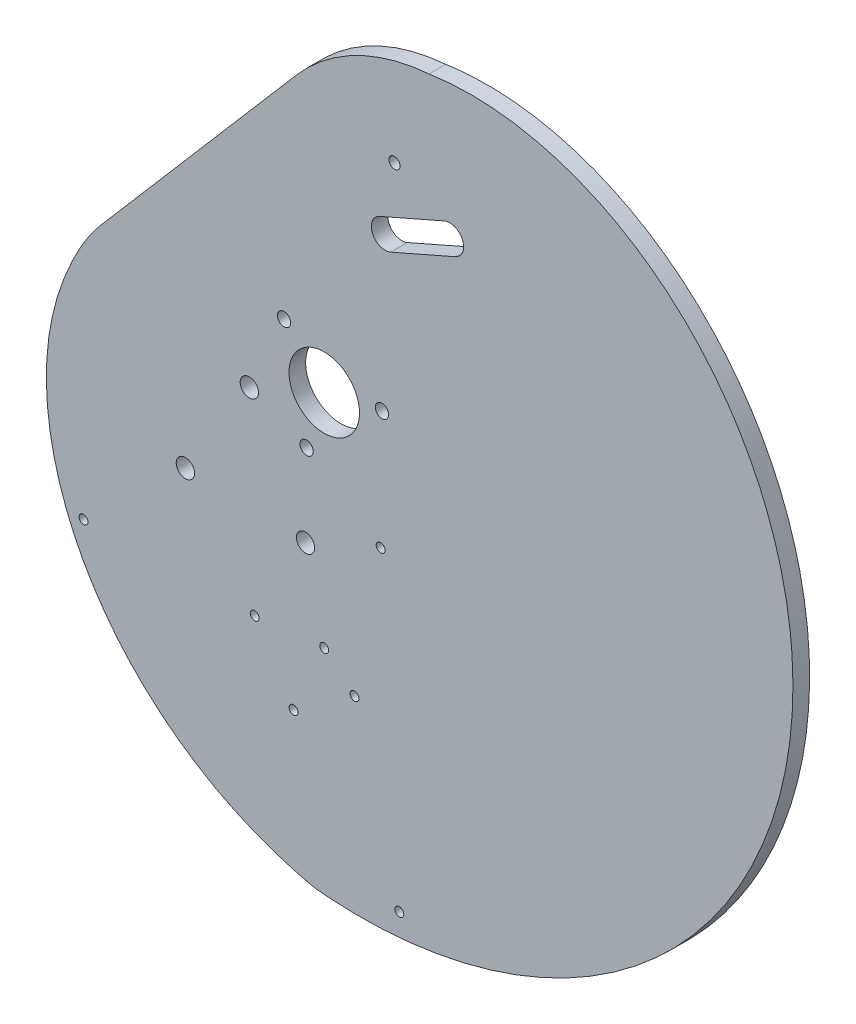
SolidWorks part; units mm, degrees
ref_plane "Front Plane" through (0, 0, 0) normal (0, 0, 1) x (1, 0, 0)
ref_plane "Top Plane" through (0, 0, 0) normal (0, 1, 0) x (1, 0, 0)
ref_plane "Right Plane" through (0, 0, 0) normal (1, 0, 0) x (0, 0, -1)
curve "Curve1"
sketch "Sketch1" plane through (0, 0, 0) normal (0, 0, 1) x (1, 0, 0)
  line L0 (10.9805, 30.1851) -> (22.6104, 35.2876) construction
  line L1 (9.976, 32.4744) -> (21.6059, 37.5769)
  line L2 (11.9849, 27.8957) -> (23.6148, 32.9983)
  line L3 (10.7688, 46.4724) -> (16.7954, 32.7363) construction
  line L4 (-15.5247, -36.542) -> (-17.0714, -47.8252) construction
  line L5 (-12.072, -37.0153) -> (-13.6188, -48.2986) construction
  line L6 (-18.9773, -36.0687) -> (-20.5241, -47.3519) construction
  line L7 (-15.1851, -34.0651) -> (-15.8642, -39.0188) construction
  line L8 (5.6152, 38.2953) -> (3.8561, 42.4197)
  line L9 (20.342, 44.5764) -> (18.4912, 48.9157)
  circle A0 centre (0, 0) radius 6.35
  arc A1 (9.976, 32.4744) -> (11.9849, 27.8957) centre (10.9805, 30.1851) ccw
  arc A2 (23.6148, 32.9983) -> (21.6059, 37.5769) centre (22.6104, 35.2876) ccw
  arc A3 (5.6152, 38.2953) -> (20.342, 44.5764) centre (12.9786, 41.4359) ccw
  arc A4 (-12.072, -37.0153) -> (-18.9773, -36.0687) centre (-15.5247, -36.542) ccw construction
  arc A5 (-20.5241, -47.3519) -> (-13.6188, -48.2986) centre (-17.0714, -47.8252) ccw construction
  spline S0 degree 3 poles (-1.1843, -67.9504) (-0.014, -68.2767) (1.195, -68.3213) (2.3889, -68.4148) (3.5889, -68.4701) (4.791, -68.5105) (5.9959, -68.5295) (7.203, -68.5287) (8.412, -68.5074) (9.6226, -68.4657) (10.8344, -68.4032) (12.047, -68.32) (13.2602, -68.2159) (14.4735, -68.0908) (15.6866, -67.9446) (16.8991, -67.777) (18.1106, -67.5882) (19.3207, -67.3779) (20.529, -67.1461) (21.7351, -66.8927) (22.9386, -66.6176) (24.1392, -66.3208) (25.3362, -66.0022) (26.5295, -65.6619) (27.7184, -65.2996) (28.9026, -64.9155) (30.0816, -64.5096) (31.2551, -64.0817) (32.4225, -63.632) (33.5833, -63.1604) (34.7372, -62.667) (35.8837, -62.1518) (37.0223, -61.6149) (38.1525, -61.0563) (39.2739, -60.4761) (40.3861, -59.8743) (41.4885, -59.2512) (42.5806, -58.6068) (43.6621, -57.9411) (44.7324, -57.2544) (45.791, -56.5468) (46.8375, -55.8184) (47.8714, -55.0695) (48.8923, -54.3001) (49.8996, -53.5105) (50.8929, -52.7009) (51.8717, -51.8715) (52.8356, -51.0225) (53.7841, -50.1542) (54.7166, -49.2668) (55.6329, -48.3607) (56.5323, -47.436) (57.4145, -46.4932) (58.279, -45.5324) (59.1254, -44.554) (59.9531, -43.5583) (60.7619, -42.5458) (61.5512, -41.5167) (62.3207, -40.4714) (63.0698, -39.4103) (63.7983, -38.3338) (64.5057, -37.2423) (65.1916, -36.1362) (65.8556, -35.016) (66.4973, -33.882) (67.1165, -32.7348) (67.7126, -31.5748) (68.2854, -30.4026) (68.8345, -29.2185) (69.3596, -28.023) (69.8603, -26.8168) (70.3364, -25.6003) (70.7876, -24.3741) (71.2134, -23.1386) (71.6138, -21.8945) (71.9884, -20.6423) (72.337, -19.3826) (72.6592, -18.116) (72.955, -16.843) (73.224, -15.5643) (73.4661, -14.2804) (73.6812, -12.992) (73.8689, -11.6997) (74.0292, -10.4042) (74.1619, -9.106) (74.2669, -7.8058) (74.3441, -6.5043) (74.3933, -5.2021) (74.4146, -3.9) (74.4078, -2.5984) (74.3729, -1.2982) (74.3098, -0.0001) (74.2186, 1.2954) (74.0993, 2.5875) (73.9518, 3.8756) (73.7762, 5.1589) (73.5725, 6.4367) (73.3409, 7.7084) (73.0814, 8.9732) (72.7942, 10.2305) (72.4792, 11.4795) (72.1368, 12.7196) (71.767, 13.95) (71.3701, 15.1701) (70.9462, 16.3792) (70.4955, 17.5765) (70.0184, 18.7613) (69.515, 19.9331) (68.9856, 21.091) (68.4305, 22.2344) (67.85, 23.3626) (67.2445, 24.475) (66.6143, 25.5709) (65.9598, 26.6495) (65.2813, 27.7103) (64.5793, 28.7526) (63.8542, 29.7758) (63.1064, 30.7792) (62.3364, 31.7621) (61.5447, 32.7241) (60.7318, 33.6643) (59.8981, 34.5824) (59.0442, 35.4776) (58.1707, 36.3494) (57.2782, 37.1972) (56.3671, 38.0204) (55.4383, 38.8186) (54.4923, 39.5913) (53.53, 40.3381) (52.552, 41.0585) (51.5591, 41.7521) (50.552, 42.4186) (49.5315, 43.0576) (48.4984, 43.6687) (47.4535, 44.2516) (46.3974, 44.8061) (45.3311, 45.3318) (44.2553, 45.8284) (43.1709, 46.2958) (42.0786, 46.7338) (40.9793, 47.1421) (39.8737, 47.5205) (38.7628, 47.869) (37.6473, 48.1874) (36.5281, 48.4755) (35.4061, 48.7334) (34.282, 48.961) (33.1567, 49.1581) (32.031, 49.3249) (30.9059, 49.4613) (29.7821, 49.5673) (28.6604, 49.6431) (27.5418, 49.6886) (26.427, 49.7041) (25.3169, 49.6895) (24.2124, 49.6451) (23.1141, 49.571) (22.0231, 49.4674) (20.94, 49.3346) (19.8657, 49.1727) (18.801, 48.982) (17.7468, 48.7628) (16.7037, 48.5154) (15.6726, 48.2401) (14.6543, 47.9373) (13.6495, 47.6073) (12.659, 47.2504) (11.6836, 46.8672) (10.7239, 46.458) (9.7807, 46.0233) (8.8547, 45.5635) (7.9467, 45.0791) (7.0573, 44.5706) (6.1871, 44.0386) (5.3369, 43.4835) (4.5074, 42.906) (3.699, 42.3065) (2.9126, 41.6858) (2.1491, 41.0448) (1.4087, 40.3857) (0.692, 39.711) (-0.0007, 39.0233) (-0.6692, 38.3252) (-1.3135, 37.6192) (-1.9336, 36.908) (-2.5298, 36.194) (-3.1024, 35.4799) (-3.6521, 34.7682) (-4.1795, 34.0612) (-4.6854, 33.3616) (-5.1709, 32.6716) (-5.637, 31.9937) (-6.085, 31.3301) (-6.5163, 30.6831) (-6.9325, 30.0548) (-7.3352, 29.4474) (-7.7263, 28.8629) (-8.1078, 28.3032) (-8.4816, 27.77) (-8.8501, 27.2652) (-9.216, 26.7897) (-9.5801, 26.3424) (-9.9432, 25.9213) (-10.3062, 25.5243) (-10.6698, 25.1494) (-11.0346, 24.7946) (-11.4009, 24.4578) (-11.7691, 24.1369) (-12.1394, 23.8299) (-12.5117, 23.5348) (-12.8861, 23.2497) (-13.2622, 22.9725) (-13.6397, 22.7014) (-14.0182, 22.4345) (-14.3971, 22.1699) (-14.7757, 21.906) (-15.1531, 21.6409) (-15.5285, 21.3732) (-15.9009, 21.1012) (-16.269, 20.8234) (-16.6317, 20.5384) (-16.9875, 20.2449) (-17.3351, 19.9417) (-17.6745, 19.6295) (-18.0059, 19.3089) (-18.3295, 18.9807) (-18.6455, 18.6455) (-18.9542, 18.3039) (-19.2559, 17.9565) (-19.5509, 17.6038) (-19.8396, 17.2464) (-20.1224, 16.8848) (-20.3997, 16.5195) (-20.672, 16.1508) (-20.9397, 15.7793) (-21.2033, 15.4052) (-21.4634, 15.0289) (-21.7205, 14.6507) (-21.9753, 14.2708) (-22.2281, 13.8895) (-22.4798, 13.507) (-22.7308, 13.1233) (-22.9819, 12.7386) (-23.2336, 12.3529) (-23.4866, 11.9663) (-23.7416, 11.5787) (-23.9993, 11.19) (-24.2602, 10.8001) (-24.5251, 10.4088) (-24.7947, 10.016) (-25.0696, 9.6214) (-25.3504, 9.2246) (-25.6379, 8.8254) (-25.9327, 8.4234) (-26.2354, 8.018) (-26.5467, 7.609) (-26.8672, 7.1956) (-27.1974, 6.7776) (-27.537, 6.3539) (-27.8856, 5.9238) (-28.2424, 5.4864) (-28.6069, 5.0408) (-28.9783, 4.5865) (-29.3562, 4.1226) (-29.7396, 3.6485) (-30.1278, 3.1637) (-30.5202, 2.6674) (-30.9158, 2.1592) (-31.314, 1.6386) (-31.7137, 1.1051) (-32.1143, 0.5583) (-32.5148, -0.0021) (-32.9143, -0.5765) (-33.3119, -1.1651) (-33.7067, -1.7682) (-34.0978, -2.3859) (-34.4843, -3.0184) (-34.8652, -3.6658) (-35.2396, -4.3281) (-35.6066, -5.0053) (-35.9651, -5.6973) (-36.3143, -6.404) (-36.6531, -7.1254) (-36.9808, -7.8611) (-37.2963, -8.611) (-37.5988, -9.3748) (-37.8873, -10.1521) (-38.1609, -10.9426) (-38.4187, -11.7459) (-38.66, -12.5613) (-38.8837, -13.3886) (-39.0892, -14.2271) (-39.2755, -15.0762) (-39.4422, -15.9354) (-39.589, -16.8043) (-39.7155, -17.6823) (-39.8215, -18.5689) (-39.9067, -19.4636) (-39.9709, -20.366) (-40.0137, -21.2755) (-40.035, -22.1916) (-40.0345, -23.1138) (-40.0119, -24.0415) (-39.9672, -24.9742) (-39.9002, -25.9114) (-39.8105, -26.8525) (-39.6982, -27.7969) (-39.563, -28.7442) (-39.4048, -29.6936) (-39.2235, -30.6448) (-39.019, -31.597) (-38.7911, -32.5497) (-38.5399, -33.5023) (-38.2653, -34.4543) (-37.9672, -35.4051) (-37.6456, -36.354) (-37.3004, -37.3005) (-36.9317, -38.2441) (-36.5395, -39.184) (-36.1238, -40.1197) (-35.6847, -41.0507) (-35.2221, -41.9763) (-34.7363, -42.896) (-34.2272, -43.8091) (-33.695, -44.715) (-33.1398, -45.6133) (-32.5617, -46.5032) (-31.9609, -47.3843) (-31.3375, -48.2559) (-30.6917, -49.1174) (-30.0238, -49.9683) (-29.3338, -50.808) (-28.6221, -51.636) (-27.8888, -52.4517) (-27.1343, -53.2545) (-26.3587, -54.0439) (-25.5624, -54.8193) (-24.7457, -55.5802) (-23.9088, -56.3261) (-23.0521, -57.0564) (-22.1759, -57.7707) (-21.2805, -58.4684) (-20.3664, -59.149) (-19.4339, -59.812) (-18.4833, -60.4569) (-17.5151, -61.0833) (-16.5298, -61.6908) (-15.5276, -62.2787) (-14.5091, -62.8467) (-13.4747, -63.3944) (-12.4248, -63.9213) (-11.36, -64.4271) (-10.2807, -64.9112) (-9.1874, -65.3733) (-8.0806, -65.8131) (-6.9608, -66.2301) (-5.8286, -66.6239) (-4.6845, -66.9947) (-3.5289, -67.3403) (-2.3631, -67.6669) (-1.1843, -67.9504) (-0.014, -68.2767) (1.195, -68.3213) knots -0.0101 -0.006743 -0.003377 0 0.00332 0.006645 0.009976 0.013312 0.016655 0.020003 0.023357 0.026716 0.030082 0.033453 0.036831 0.040214 0.043603 0.046998 0.050399 0.053806 0.057218 0.060637 0.064061 0.067491 0.070927 0.074369 0.077816 0.081269 0.084728 0.088192 0.091662 0.095138 0.098619 0.102105 0.105597 0.109094 0.112596 0.116103 0.119615 0.123133 0.126655 0.130182 0.133714 0.137251 0.140792 0.144337 0.147888 0.151442 0.155 0.158563 0.16213 0.1657 0.169275 0.172853 0.176434 0.180019 0.183607 0.187199 0.190793 0.19439 0.19799 0.201593 0.205199 0.208806 0.212416 0.216028 0.219642 0.223258 0.226875 0.230494 0.234115 0.237736 0.241359 0.244982 0.248606 0.252231 0.255856 0.259481 0.263106 0.266731 0.270356 0.273981 0.277605 0.281228 0.28485 0.28847 0.29209 0.295708 0.299324 0.302939 0.306551 0.310161 0.313769 0.317374 0.320976 0.324575 0.328171 0.331763 0.335352 0.338938 0.342519 0.346096 0.349669 0.353237 0.356801 0.360359 0.363913 0.367461 0.371004 0.374541 0.378073 0.381598 0.385117 0.38863 0.392136 0.395636 0.399128 0.402614 0.406092 0.409563 0.413026 0.416482 0.419929 0.423369 0.4268 0.430223 0.433637 0.437043 0.44044 0.443828 0.447206 0.450575 0.453935 0.457284 0.460624 0.463953 0.467272 0.47058 0.473877 0.477164 0.480439 0.483703 0.486955 0.490196 0.493426 0.496643 0.499848 0.503042 0.506223 0.509391 0.512547 0.515691 0.518822 0.52194 0.525045 0.528137 0.531216 0.534282 0.537335 0.540375 0.543401 0.546414 0.549414 0.5524 0.555374 0.558333 0.56128 0.564213 0.567133 0.57004 0.572933 0.575814 0.578681 0.581535 0.584377 0.587205 0.590021 0.592825 0.595616 0.598394 0.60116 0.603911 0.606642 0.60935 0.612032 0.614684 0.617303 0.619884 0.622424 0.62492 0.627367 0.629763 0.632104 0.634387 0.636609 0.638767 0.640858 0.64288 0.644831 0.64671 0.648517 0.65025 0.651911 0.653509 0.655048 0.656538 0.657984 0.659394 0.660772 0.662125 0.663458 0.664774 0.666078 0.667373 0.668662 0.669946 0.671227 0.672507 0.673786 0.675065 0.676344 0.677623 0.678903 0.680182 0.681461 0.68274 0.684019 0.685298 0.686575 0.687853 0.689129 0.690404 0.691679 0.692952 0.694224 0.695495 0.696765 0.698035 0.699304 0.700572 0.70184 0.703109 0.704379 0.705651 0.706925 0.708202 0.709483 0.71077 0.712063 0.713364 0.714674 0.715995 0.717328 0.718676 0.72004 0.721422 0.722825 0.72425 0.7257 0.727177 0.728683 0.730218 0.731784 0.73338 0.735008 0.736668 0.738359 0.740082 0.741837 0.743623 0.745441 0.747291 0.749171 0.751082 0.753022 0.754993 0.756992 0.759021 0.761077 0.76316 0.765271 0.767407 0.769569 0.771756 0.773967 0.776201 0.778458 0.780736 0.783036 0.785357 0.787697 0.790056 0.792433 0.794828 0.797239 0.799666 0.80211 0.804571 0.807047 0.80954 0.812049 0.814575 0.817116 0.819674 0.822248 0.824838 0.827444 0.830066 0.832704 0.835358 0.838027 0.840713 0.843414 0.846131 0.848864 0.851612 0.854376 0.857155 0.859949 0.862759 0.865584 0.868424 0.871279 0.874149 0.877033 0.879933 0.882847 0.885776 0.88872 0.891678 0.89465 0.897636 0.900637 0.903651 0.906679 0.909721 0.912777 0.915847 0.91893 0.922026 0.925135 0.928258 0.931393 0.934541 0.937702 0.940876 0.944062 0.947261 0.950471 0.953694 0.956929 0.960175 0.963433 0.966703 0.969984 0.973276 0.976579 0.979893 0.983218 0.986554 0.9899 0.993257 0.996623 1 1.00332 1.006645 1.009976 only from (0, -68.2309) to (0, -68.2309) construction
  spline S1 degree 3 poles (-1.1843, -67.9504) (-0.014, -68.2767) (1.195, -68.3213) (2.3889, -68.4148) (3.5889, -68.4701) (4.791, -68.5105) (5.9959, -68.5295) (7.203, -68.5287) (8.412, -68.5074) (9.6226, -68.4657) (10.8344, -68.4032) (12.047, -68.32) (13.2602, -68.2159) (14.4735, -68.0908) (15.6866, -67.9446) (16.8991, -67.777) (18.1106, -67.5882) (19.3207, -67.3779) (20.529, -67.1461) (21.7351, -66.8927) (22.9386, -66.6176) (24.1392, -66.3208) (25.3362, -66.0022) (26.5295, -65.6619) (27.7184, -65.2996) (28.9026, -64.9155) (30.0816, -64.5096) (31.2551, -64.0817) (32.4225, -63.632) (33.5833, -63.1604) (34.7372, -62.667) (35.8837, -62.1518) (37.0223, -61.6149) (38.1525, -61.0563) (39.2739, -60.4761) (40.3861, -59.8743) (41.4885, -59.2512) (42.5806, -58.6068) (43.6621, -57.9411) (44.7324, -57.2544) (45.791, -56.5468) (46.8375, -55.8184) (47.8714, -55.0695) (48.8923, -54.3001) (49.8996, -53.5105) (50.8929, -52.7009) (51.8717, -51.8715) (52.8356, -51.0225) (53.7841, -50.1542) (54.7166, -49.2668) (55.6329, -48.3607) (56.5323, -47.436) (57.4145, -46.4932) (58.279, -45.5324) (59.1254, -44.554) (59.9531, -43.5583) (60.7619, -42.5458) (61.5512, -41.5167) (62.3207, -40.4714) (63.0698, -39.4103) (63.7983, -38.3338) (64.5057, -37.2423) (65.1916, -36.1362) (65.8556, -35.016) (66.4973, -33.882) (67.1165, -32.7348) (67.7126, -31.5748) (68.2854, -30.4026) (68.8345, -29.2185) (69.3596, -28.023) (69.8603, -26.8168) (70.3364, -25.6003) (70.7876, -24.3741) (71.2134, -23.1386) (71.6138, -21.8945) (71.9884, -20.6423) (72.337, -19.3826) (72.6592, -18.116) (72.955, -16.843) (73.224, -15.5643) (73.4661, -14.2804) (73.6812, -12.992) (73.8689, -11.6997) (74.0292, -10.4042) (74.1619, -9.106) (74.2669, -7.8058) (74.3441, -6.5043) (74.3933, -5.2021) (74.4146, -3.9) (74.4078, -2.5984) (74.3729, -1.2982) (74.3098, -0.0001) (74.2186, 1.2954) (74.0993, 2.5875) (73.9518, 3.8756) (73.7762, 5.1589) (73.5725, 6.4367) (73.3409, 7.7084) (73.0814, 8.9732) (72.7942, 10.2305) (72.4792, 11.4795) (72.1368, 12.7196) (71.767, 13.95) (71.3701, 15.1701) (70.9462, 16.3792) (70.4955, 17.5765) (70.0184, 18.7613) (69.515, 19.9331) (68.9856, 21.091) (68.4305, 22.2344) (67.85, 23.3626) (67.2445, 24.475) (66.6143, 25.5709) (65.9598, 26.6495) (65.2813, 27.7103) (64.5793, 28.7526) (63.8542, 29.7758) (63.1064, 30.7792) (62.3364, 31.7621) (61.5447, 32.7241) (60.7318, 33.6643) (59.8981, 34.5824) (59.0442, 35.4776) (58.1707, 36.3494) (57.2782, 37.1972) (56.3671, 38.0204) (55.4383, 38.8186) (54.4923, 39.5913) (53.53, 40.3381) (52.552, 41.0585) (51.5591, 41.7521) (50.552, 42.4186) (49.5315, 43.0576) (48.4984, 43.6687) (47.4535, 44.2516) (46.3974, 44.8061) (45.3311, 45.3318) (44.2553, 45.8284) (43.1709, 46.2958) (42.0786, 46.7338) (40.9793, 47.1421) (39.8737, 47.5205) (38.7628, 47.869) (37.6473, 48.1874) (36.5281, 48.4755) (35.4061, 48.7334) (34.282, 48.961) (33.1567, 49.1581) (32.031, 49.3249) (30.9059, 49.4613) (29.7821, 49.5673) (28.6604, 49.6431) (27.5418, 49.6886) (26.427, 49.7041) (25.3169, 49.6895) (24.2124, 49.6451) (23.1141, 49.571) (22.0231, 49.4674) (20.94, 49.3346) (19.8657, 49.1727) (18.801, 48.982) (17.7468, 48.7628) (16.7037, 48.5154) (15.6726, 48.2401) (14.6543, 47.9373) (13.6495, 47.6073) (12.659, 47.2504) (11.6836, 46.8672) (10.7239, 46.458) (9.7807, 46.0233) (8.8547, 45.5635) (7.9467, 45.0791) (7.0573, 44.5706) (6.1871, 44.0386) (5.3369, 43.4835) (4.5074, 42.906) (3.699, 42.3065) (2.9126, 41.6858) (2.1491, 41.0448) (1.4087, 40.3857) (0.692, 39.711) (-0.0007, 39.0233) (-0.6692, 38.3252) (-1.3135, 37.6192) (-1.9336, 36.908) (-2.5298, 36.194) (-3.1024, 35.4799) (-3.6521, 34.7682) (-4.1795, 34.0612) (-4.6854, 33.3616) (-5.1709, 32.6716) (-5.637, 31.9937) (-6.085, 31.3301) (-6.5163, 30.6831) (-6.9325, 30.0548) (-7.3352, 29.4474) (-7.7263, 28.8629) (-8.1078, 28.3032) (-8.4816, 27.77) (-8.8501, 27.2652) (-9.216, 26.7897) (-9.5801, 26.3424) (-9.9432, 25.9213) (-10.3062, 25.5243) (-10.6698, 25.1494) (-11.0346, 24.7946) (-11.4009, 24.4578) (-11.7691, 24.1369) (-12.1394, 23.8299) (-12.5117, 23.5348) (-12.8861, 23.2497) (-13.2622, 22.9725) (-13.6397, 22.7014) (-14.0182, 22.4345) (-14.3971, 22.1699) (-14.7757, 21.906) (-15.1531, 21.6409) (-15.5285, 21.3732) (-15.9009, 21.1012) (-16.269, 20.8234) (-16.6317, 20.5384) (-16.9875, 20.2449) (-17.3351, 19.9417) (-17.6745, 19.6295) (-18.0059, 19.3089) (-18.3295, 18.9807) (-18.6455, 18.6455) (-18.9542, 18.3039) (-19.2559, 17.9565) (-19.5509, 17.6038) (-19.8396, 17.2464) (-20.1224, 16.8848) (-20.3997, 16.5195) (-20.672, 16.1508) (-20.9397, 15.7793) (-21.2033, 15.4052) (-21.4634, 15.0289) (-21.7205, 14.6507) (-21.9753, 14.2708) (-22.2281, 13.8895) (-22.4798, 13.507) (-22.7308, 13.1233) (-22.9819, 12.7386) (-23.2336, 12.3529) (-23.4866, 11.9663) (-23.7416, 11.5787) (-23.9993, 11.19) (-24.2602, 10.8001) (-24.5251, 10.4088) (-24.7947, 10.016) (-25.0696, 9.6214) (-25.3504, 9.2246) (-25.6379, 8.8254) (-25.9327, 8.4234) (-26.2354, 8.018) (-26.5467, 7.609) (-26.8672, 7.1956) (-27.1974, 6.7776) (-27.537, 6.3539) (-27.8856, 5.9238) (-28.2424, 5.4864) (-28.6069, 5.0408) (-28.9783, 4.5865) (-29.3562, 4.1226) (-29.7396, 3.6485) (-30.1278, 3.1637) (-30.5202, 2.6674) (-30.9158, 2.1592) (-31.314, 1.6386) (-31.7137, 1.1051) (-32.1143, 0.5583) (-32.5148, -0.0021) (-32.9143, -0.5765) (-33.3119, -1.1651) (-33.7067, -1.7682) (-34.0978, -2.3859) (-34.4843, -3.0184) (-34.8652, -3.6658) (-35.2396, -4.3281) (-35.6066, -5.0053) (-35.9651, -5.6973) (-36.3143, -6.404) (-36.6531, -7.1254) (-36.9808, -7.8611) (-37.2963, -8.611) (-37.5988, -9.3748) (-37.8873, -10.1521) (-38.1609, -10.9426) (-38.4187, -11.7459) (-38.66, -12.5613) (-38.8837, -13.3886) (-39.0892, -14.2271) (-39.2755, -15.0762) (-39.4422, -15.9354) (-39.589, -16.8043) (-39.7155, -17.6823) (-39.8215, -18.5689) (-39.9067, -19.4636) (-39.9709, -20.366) (-40.0137, -21.2755) (-40.035, -22.1916) (-40.0345, -23.1138) (-40.0119, -24.0415) (-39.9672, -24.9742) (-39.9002, -25.9114) (-39.8105, -26.8525) (-39.6982, -27.7969) (-39.563, -28.7442) (-39.4048, -29.6936) (-39.2235, -30.6448) (-39.019, -31.597) (-38.7911, -32.5497) (-38.5399, -33.5023) (-38.2653, -34.4543) (-37.9672, -35.4051) (-37.6456, -36.354) (-37.3004, -37.3005) (-36.9317, -38.2441) (-36.5395, -39.184) (-36.1238, -40.1197) (-35.6847, -41.0507) (-35.2221, -41.9763) (-34.7363, -42.896) (-34.2272, -43.8091) (-33.695, -44.715) (-33.1398, -45.6133) (-32.5617, -46.5032) (-31.9609, -47.3843) (-31.3375, -48.2559) (-30.6917, -49.1174) (-30.0238, -49.9683) (-29.3338, -50.808) (-28.6221, -51.636) (-27.8888, -52.4517) (-27.1343, -53.2545) (-26.3587, -54.0439) (-25.5624, -54.8193) (-24.7457, -55.5802) (-23.9088, -56.3261) (-23.0521, -57.0564) (-22.1759, -57.7707) (-21.2805, -58.4684) (-20.3664, -59.149) (-19.4339, -59.812) (-18.4833, -60.4569) (-17.5151, -61.0833) (-16.5298, -61.6908) (-15.5276, -62.2787) (-14.5091, -62.8467) (-13.4747, -63.3944) (-12.4248, -63.9213) (-11.36, -64.4271) (-10.2807, -64.9112) (-9.1874, -65.3733) (-8.0806, -65.8131) (-6.9608, -66.2301) (-5.8286, -66.6239) (-4.6845, -66.9947) (-3.5289, -67.3403) (-2.3631, -67.6669) (-1.1843, -67.9504) (-0.014, -68.2767) (1.195, -68.3213) knots -0.0101 -0.006743 -0.003377 0 0.00332 0.006645 0.009976 0.013312 0.016655 0.020003 0.023357 0.026716 0.030082 0.033453 0.036831 0.040214 0.043603 0.046998 0.050399 0.053806 0.057218 0.060637 0.064061 0.067491 0.070927 0.074369 0.077816 0.081269 0.084728 0.088192 0.091662 0.095138 0.098619 0.102105 0.105597 0.109094 0.112596 0.116103 0.119615 0.123133 0.126655 0.130182 0.133714 0.137251 0.140792 0.144337 0.147888 0.151442 0.155 0.158563 0.16213 0.1657 0.169275 0.172853 0.176434 0.180019 0.183607 0.187199 0.190793 0.19439 0.19799 0.201593 0.205199 0.208806 0.212416 0.216028 0.219642 0.223258 0.226875 0.230494 0.234115 0.237736 0.241359 0.244982 0.248606 0.252231 0.255856 0.259481 0.263106 0.266731 0.270356 0.273981 0.277605 0.281228 0.28485 0.28847 0.29209 0.295708 0.299324 0.302939 0.306551 0.310161 0.313769 0.317374 0.320976 0.324575 0.328171 0.331763 0.335352 0.338938 0.342519 0.346096 0.349669 0.353237 0.356801 0.360359 0.363913 0.367461 0.371004 0.374541 0.378073 0.381598 0.385117 0.38863 0.392136 0.395636 0.399128 0.402614 0.406092 0.409563 0.413026 0.416482 0.419929 0.423369 0.4268 0.430223 0.433637 0.437043 0.44044 0.443828 0.447206 0.450575 0.453935 0.457284 0.460624 0.463953 0.467272 0.47058 0.473877 0.477164 0.480439 0.483703 0.486955 0.490196 0.493426 0.496643 0.499848 0.503042 0.506223 0.509391 0.512547 0.515691 0.518822 0.52194 0.525045 0.528137 0.531216 0.534282 0.537335 0.540375 0.543401 0.546414 0.549414 0.5524 0.555374 0.558333 0.56128 0.564213 0.567133 0.57004 0.572933 0.575814 0.578681 0.581535 0.584377 0.587205 0.590021 0.592825 0.595616 0.598394 0.60116 0.603911 0.606642 0.60935 0.612032 0.614684 0.617303 0.619884 0.622424 0.62492 0.627367 0.629763 0.632104 0.634387 0.636609 0.638767 0.640858 0.64288 0.644831 0.64671 0.648517 0.65025 0.651911 0.653509 0.655048 0.656538 0.657984 0.659394 0.660772 0.662125 0.663458 0.664774 0.666078 0.667373 0.668662 0.669946 0.671227 0.672507 0.673786 0.675065 0.676344 0.677623 0.678903 0.680182 0.681461 0.68274 0.684019 0.685298 0.686575 0.687853 0.689129 0.690404 0.691679 0.692952 0.694224 0.695495 0.696765 0.698035 0.699304 0.700572 0.70184 0.703109 0.704379 0.705651 0.706925 0.708202 0.709483 0.71077 0.712063 0.713364 0.714674 0.715995 0.717328 0.718676 0.72004 0.721422 0.722825 0.72425 0.7257 0.727177 0.728683 0.730218 0.731784 0.73338 0.735008 0.736668 0.738359 0.740082 0.741837 0.743623 0.745441 0.747291 0.749171 0.751082 0.753022 0.754993 0.756992 0.759021 0.761077 0.76316 0.765271 0.767407 0.769569 0.771756 0.773967 0.776201 0.778458 0.780736 0.783036 0.785357 0.787697 0.790056 0.792433 0.794828 0.797239 0.799666 0.80211 0.804571 0.807047 0.80954 0.812049 0.814575 0.817116 0.819674 0.822248 0.824838 0.827444 0.830066 0.832704 0.835358 0.838027 0.840713 0.843414 0.846131 0.848864 0.851612 0.854376 0.857155 0.859949 0.862759 0.865584 0.868424 0.871279 0.874149 0.877033 0.879933 0.882847 0.885776 0.88872 0.891678 0.89465 0.897636 0.900637 0.903651 0.906679 0.909721 0.912777 0.915847 0.91893 0.922026 0.925135 0.928258 0.931393 0.934541 0.937702 0.940876 0.944062 0.947261 0.950471 0.953694 0.956929 0.960175 0.963433 0.966703 0.969984 0.973276 0.976579 0.979893 0.983218 0.986554 0.9899 0.993257 0.996623 1 1.00332 1.006645 1.009976 only from (0, -68.2309) to (0, -68.2309)
  point P6 (16.7954, 32.7363)
  point P18 (-16.298, -42.1836)
  dimension "D1" = 12.7
  dimension "D5" = 5.5
  dimension "D2" = 12.7
  dimension "D3" = 5
  dimension "D4" = 15
extrude "Boss-Extrude1" add sketch "Sketch1" along normal mid plane 3 contours A3 S1 A0 A2 L2 A1 L1
sketch "Sketch2" plane through (0, 0, 0) normal (0, 0, 1) x (1, 0, 0)
  line L0 (4.6222, 43.3119) -> (-35.7001, -3.6508) construction
  line L1 (-35.7001, -3.6508) -> (-7.0727, 43.3119)
  line L2 (-7.0727, 43.3119) -> (4.6222, 43.3119)
  line L3 (7.6571, 40.7062) -> (-41.2002, -16.1969)
  line L4 (4.6222, 43.3119) -> (7.6571, 40.7062)
  line L5 (-35.7001, -3.6508) -> (-41.2002, -16.1969)
extrude "Cut-Extrude1" cut sketch "Sketch2" against normal through all both and the other way through all
fillet "Fillet1" radius 20 1 edges at (-38.9189, -13.5399, 0)
sketch "Sketch3" plane through (0, 0, 1.5) normal (0, 0, 1) x (1, 0, 0)
  point P0 (-13.488, -5.936)
  point P1 (-3.3675, -25.0764)
  point P3 (-25.0038, -24.2708)
fillet "Fillet2" [suppressed] radius 2.5
fillet "Fillet3" [suppressed] radius 1
sketch "Sketch6" plane through (0, 0, 0) normal (0, 0, 1) x (1, 0, 0)
  line L2 (-40.2409, 5.985) -> (-5.0109, 47.0167)
  line L3 (-40.2409, 5.985) -> (-5.0109, 47.0167)
  arc A1 (-5.0109, 47.0167) -> (18.8738, 59.1348) centre (21.5961, 24.1717) cw
  arc A2 (-40.2409, 5.985) -> (-43.3928, 1.5586) centre (-17.4796, -13.5579) ccw
  arc A3 (-40.2409, 5.985) -> (-43.3928, 1.5586) centre (-17.4796, -13.5579) ccw
  spline S2 degree 3 poles (30414.9948, -18924.8779) (-757.4347, -1926.1501) (-235.029, 77.1027) (33.4507, 59.3461) (37.0313, 58.7272) (43.9674, 56.8115) (47.3229, 55.515) (53.7078, 52.3312) (56.7371, 50.4441) (62.3895, 46.1692) (65.0134, 43.7791) (69.7846, 38.6064) (71.9342, 35.8236) (75.7327, 29.9643) (77.3816, 26.8878) (80.1644, 20.5326) (81.2983, 17.2539) (83.0485, 10.579) (83.6648, 7.183) (84.3866, 0.3517) (84.4921, -3.0835) (84.2072, -9.921) (83.8168, -13.3233) (82.562, -20.0286) (81.6977, -23.3317) (78.4358, -33.0013) (75.367, -39.1258) (67.7295, -50.3171) (63.1613, -55.384) (52.8841, -64.1458) (47.1758, -67.8403) (35.0265, -73.6501) (28.5867, -75.7651) (18.7016, -77.6861) (15.3691, -78.1188) (10.3543, -78.4567) (8.6797, -78.5176) (6.5875, -78.5294) (6.1701, -78.5285) (5.3343, -78.5205) (4.9137, -78.5133) (4.072, -78.492) (3.6586, -78.4781) (3.0497, -78.4542) (2.8432, -78.4455) (2.4135, -78.4255) (2.1919, -78.4141) (1.8492, -78.3942) (1.7308, -78.3869) (1.5098, -78.3725) (1.4058, -78.3654) (1.1132, -78.3453) (0.944, -78.3334) (0.7644, -78.3218) (0.7301, -78.3196) (0.6646, -78.3156) (0.6353, -78.3139) (0.5391, -78.3084) (0.4507, -78.3038) (0.1135, -78.285) (-0.2076, -78.2671) (-0.8333, -78.2062) (-1.0659, -78.1799) (-1.4499, -78.1259) (-1.5869, -78.1048) (-1.8434, -78.0619) (-1.9656, -78.0398) (-2.5465, -77.9285) (-2.9147, -77.8384) (-3.3304, -77.7331) (-3.4462, -77.7027) (-3.5862, -77.666) (-3.6273, -77.6553) (-3.6982, -77.6367) (-3.7277, -77.6291) (-3.8942, -77.5863) (-4.2091, -77.5075) (-4.6212, -77.4044) (-4.966, -77.3149) (-5.0818, -77.2843) (-5.3074, -77.2239) (-5.6407, -77.1332) (-5.9586, -77.0433) (-6.369, -76.9253) (-6.5693, -76.8669) (-7.1822, -76.6851) (-7.5996, -76.5573) (-8.4299, -76.2933) (-8.8413, -76.1578) (-10.8906, -75.4606) (-12.5146, -74.8354) (-15.706, -73.4558) (-17.2758, -72.7006) (-21.8904, -70.2423) (-24.8406, -68.3459) (-30.3947, -64.0648) (-32.9986, -61.6801) (-37.7616, -56.4643) (-39.9206, -53.6333) (-43.6909, -47.5866) (-45.3021, -44.3706) (-47.8702, -37.6402) (-48.8271, -34.1252) (-49.9786, -26.9144) (-50.173, -23.218) (-49.8137, -17.6585) (-49.5855, -15.8032) (-49.0714, -13.0362) (-48.8708, -12.115) (-48.4149, -10.2934) (-48.1596, -9.3921) (-47.3164, -6.7212) (-46.6509, -4.9846) (41.5832, 191.7576) (1322.0433, -365.3249) (-30605.0699, -18938.9752) knots -2.249743 -2.249743 -2.249743 -2.249743 0.03125 0.03125 0.0625 0.0625 0.09375 0.09375 0.125 0.125 0.15625 0.15625 0.1875 0.1875 0.21875 0.21875 0.25 0.25 0.28125 0.28125 0.3125 0.3125 0.34375 0.34375 0.375 0.375 0.4375 0.4375 0.5 0.5 0.5625 0.5625 0.625 0.625 0.65625 0.65625 0.671875 0.671875 0.675781 0.675781 0.679687 0.679687 0.683594 0.683594 0.685547 0.685547 0.6875 0.6875 0.688477 0.688477 0.689453 0.689453 0.691406 0.691406 0.691895 0.691895 0.692383 0.692383 0.693359 0.693359 0.695312 0.695312 0.696289 0.696289 0.696777 0.696777 0.697266 0.697266 0.699219 0.699219 0.700195 0.700195 0.700684 0.700684 0.701172 0.701172 0.703125 0.705078 0.705078 0.706055 0.706055 0.707031 0.708984 0.708984 0.710937 0.710937 0.714844 0.714844 0.71875 0.71875 0.734375 0.734375 0.75 0.75 0.78125 0.78125 0.8125 0.8125 0.84375 0.84375 0.875 0.875 0.90625 0.90625 0.9375 0.9375 0.953125 0.953125 0.960937 0.960937 0.96875 0.96875 0.984375 0.984375 2.798102 2.798102 2.798102 2.798102 only from (18.8738, 59.1348) to (-43.3928, 1.5586)
  spline S3 degree 3 poles (18.8738, 59.1348) (22.5168, 59.6868) (26.1937, 59.8261) (33.4507, 59.3461) (37.0313, 58.7272) (43.9674, 56.8115) (47.3229, 55.515) (53.7078, 52.3312) (56.7371, 50.4441) (62.3895, 46.1692) (65.0134, 43.7791) (69.7846, 38.6064) (71.9342, 35.8236) (75.7327, 29.9643) (77.3816, 26.8878) (80.1644, 20.5326) (81.2983, 17.2539) (83.0485, 10.579) (83.6648, 7.183) (84.3866, 0.3517) (84.4921, -3.0835) (84.2072, -9.921) (83.8168, -13.3233) (82.562, -20.0286) (81.6977, -23.3317) (78.4358, -33.0013) (75.367, -39.1258) (67.7295, -50.3171) (63.1613, -55.384) (52.8841, -64.1458) (47.1758, -67.8403) (35.0265, -73.6501) (28.5867, -75.7651) (18.7016, -77.6861) (15.3691, -78.1188) (10.3543, -78.4567) (8.6797, -78.5176) (6.5875, -78.5294) (6.1701, -78.5285) (5.3343, -78.5205) (4.9137, -78.5133) (4.072, -78.492) (3.6586, -78.4781) (3.0497, -78.4542) (2.8432, -78.4455) (2.4135, -78.4255) (2.1919, -78.4141) (1.8492, -78.3942) (1.7308, -78.3869) (1.5098, -78.3725) (1.4058, -78.3654) (1.1132, -78.3453) (0.944, -78.3334) (0.7644, -78.3218) (0.7301, -78.3196) (0.6646, -78.3156) (0.6353, -78.3139) (0.5391, -78.3084) (0.4507, -78.3038) (0.1135, -78.285) (-0.2076, -78.2671) (-0.8333, -78.2062) (-1.0659, -78.1799) (-1.4499, -78.1259) (-1.5869, -78.1048) (-1.8434, -78.0619) (-1.9656, -78.0398) (-2.5465, -77.9285) (-2.9147, -77.8384) (-3.3304, -77.7331) (-3.4462, -77.7027) (-3.5862, -77.666) (-3.6273, -77.6553) (-3.6982, -77.6367) (-3.7277, -77.6291) (-3.8942, -77.5863) (-4.2091, -77.5075) (-4.6212, -77.4044) (-4.966, -77.3149) (-5.0818, -77.2843) (-5.3074, -77.2239) (-5.6407, -77.1332) (-5.9586, -77.0433) (-6.369, -76.9253) (-6.5693, -76.8669) (-7.1822, -76.6851) (-7.5996, -76.5573) (-8.4299, -76.2933) (-8.8413, -76.1578) (-10.8906, -75.4606) (-12.5146, -74.8354) (-15.706, -73.4558) (-17.2758, -72.7006) (-21.8904, -70.2423) (-24.8406, -68.3459) (-30.3947, -64.0648) (-32.9986, -61.6801) (-37.7616, -56.4643) (-39.9206, -53.6333) (-43.6909, -47.5866) (-45.3021, -44.3706) (-47.8702, -37.6402) (-48.8271, -34.1252) (-49.9786, -26.9144) (-50.173, -23.218) (-49.8137, -17.6585) (-49.5855, -15.8032) (-49.0714, -13.0362) (-48.8708, -12.115) (-48.4149, -10.2934) (-48.1596, -9.3921) (-47.3164, -6.7212) (-46.6509, -4.9846) (-45.1437, -1.6238) (-44.3015, 0.0008) (-43.3928, 1.5586) knots 0 0 0 0 0.03125 0.03125 0.0625 0.0625 0.09375 0.09375 0.125 0.125 0.15625 0.15625 0.1875 0.1875 0.21875 0.21875 0.25 0.25 0.28125 0.28125 0.3125 0.3125 0.34375 0.34375 0.375 0.375 0.4375 0.4375 0.5 0.5 0.5625 0.5625 0.625 0.625 0.65625 0.65625 0.671875 0.671875 0.675781 0.675781 0.679687 0.679687 0.683594 0.683594 0.685547 0.685547 0.6875 0.6875 0.688477 0.688477 0.689453 0.689453 0.691406 0.691406 0.691895 0.691895 0.692383 0.692383 0.693359 0.693359 0.695312 0.695312 0.696289 0.696289 0.696777 0.696777 0.697266 0.697266 0.699219 0.699219 0.700195 0.700195 0.700684 0.700684 0.701172 0.701172 0.703125 0.705078 0.705078 0.706055 0.706055 0.707031 0.708984 0.708984 0.710937 0.710937 0.714844 0.714844 0.71875 0.71875 0.734375 0.734375 0.75 0.75 0.78125 0.78125 0.8125 0.8125 0.84375 0.84375 0.875 0.875 0.90625 0.90625 0.9375 0.9375 0.953125 0.953125 0.960937 0.960937 0.96875 0.96875 0.984375 0.984375 1 1 1 1
  dimension "D1" = 10
extrude "Boss-Extrude2" add sketch "Sketch6" along normal mid plane 3
sketch "Sketch7" plane through (0, 0, 0) normal (0, 0, 1) x (1, 0, 0)
  circle A0 centre (0, 0) radius 6.35
  circle A1 centre (0, 0) radius 3.175
  dimension "D1" = 6.35
extrude "Boss-Extrude3" add sketch "Sketch7" along normal mid plane 3
sketch "Sketch8" plane through (0, 0, 0) normal (0, 0, 1) x (1, 0, 0)
  line L0 (10.9805, 30.1851) -> (22.6104, 35.2876) construction
  line L1 (9.976, 32.4744) -> (21.6059, 37.5769)
  line L2 (11.9849, 27.8957) -> (23.6148, 32.9983)
  circle A0 centre (12.6554, 42.1677) radius 1
  arc A1 (5.6152, 38.2953) -> (20.342, 44.5764) centre (12.9786, 41.4359) ccw construction
  circle A2 centre (0, 0) radius 6.35
  arc A3 (9.976, 32.4744) -> (11.9849, 27.8957) centre (10.9805, 30.1851) ccw
  arc A4 (23.6148, 32.9983) -> (21.6059, 37.5769) centre (22.6104, 35.2876) ccw
  arc A5 (23.6148, 32.9983) -> (21.6059, 37.5769) centre (22.6104, 35.2876) ccw construction
  point P12 (16.7954, 32.7363)
  dimension "D2" = 2
  dimension "D1" = 0.8
extrude "Cut-Extrude2" cut sketch "Sketch8" against normal through all both and the other way through all
hole_wizard "M4 Clearance Hole1" [suppressed] positions "Sketch4" profile "Sketch5" hole size "M4" standard "ANSI Metric"
sketch "Sketch4" plane through (0, 0, 3.175) normal (0, 0, 1) x (1, 0, 0)
  point P0 (-13.488, -5.936)
  point P3 (-3.3675, -25.0764)
  point P6 (-25.0038, -24.2708)
sketch "Sketch5" plane through (-13.488, -5.936, 3.175) normal (1, 0, 0) x (0, -1, 0)
  line L0 (0, 0) -> (0, 6.35)
  line L1 (0, 6.35) -> (2.25, 6.35)
  line L2 (2.25, 6.35) -> (2.25, 0)
  line L5 (2.25, 0) -> (0, 0)
  line L11 (0, -6.35) -> (0, 107.95) construction
  dimension "Thru Hole Dia." = 4.5
  dimension "Thru Hole Depth" = 6.35
hole_wizard "M4x0.7 Tapped Hole1" positions "Sketch9" profile "Sketch11" tap size "M4x0.7" standard "ANSI Metric" end condition through all
sketch "Sketch9" plane through (0, 0, 1.5) normal (0, 0, 1) x (1, 0, 0)
  point P0 (-13.488, -5.936)
  point P3 (-25.0038, -24.2708)
  point P6 (-3.3675, -25.0764)
sketch "Sketch11" plane through (-13.488, -5.936, 1.5) normal (1, 0, 0) x (0, -1, 0)
  line L0 (0, 0) -> (0, 3.01)
  line L1 (0, 3.01) -> (1.65, 3.01)
  line L2 (1.65, 3.01) -> (1.65, 0)
  line L5 (1.65, 0) -> (0, 0)
  line L11 (0, -6.35) -> (0, 107.95) construction
  dimension "Thru Tap Drill Dia." = 3.3
  dimension "Thru Tap Drill Depth" = 3.01
cosmetic thread "Hole Thread1" parameters "D2"=4
cosmetic thread "Hole Thread2" parameters "D2"=4
cosmetic thread "Hole Thread3" parameters "D2"=4
sketch "Sketch12" plane through (0, 0, 0) normal (0, 0, 1) x (1, 0, 0)
  point P0 (-7.234, 7.8407)
  point P1 (-3.1732, -10.1851)
  point P3 (10.4072, 2.3444)
hole_wizard "M2 Clearance Hole1" positions "Sketch13" profile "Sketch14" hole size "M2" standard "ANSI Metric" end condition through all
sketch "Sketch13" plane through (0, 0, -1.5) normal (0, 0, -1) x (-1, 0, 0)
  point P0 (7.234, 7.8407)
  point P3 (3.1732, -10.1851)
  point P6 (-10.4072, 2.3444)
sketch "Sketch14" plane through (-7.234, 7.8407, -1.5) normal (1, 0, 0) x (0, 1, 0)
  line L0 (0, 0) -> (0, 3.01)
  line L1 (0, 3.01) -> (1.2, 3.01)
  line L2 (1.2, 3.01) -> (1.2, 0)
  line L5 (1.2, 0) -> (0, 0)
  line L11 (0, -6.35) -> (0, 107.95) construction
  dimension "Thru Hole Dia." = 2.4
  dimension "Thru Hole Depth" = 3.01
sketch "Sketch15" plane through (0, 0, 1.5) normal (0, 0, 1) x (1, 0, 0)
  circle A0 centre (-43.3531, -41.4597) radius 1.1
  circle A1 centre (13.5262, -74.2009) radius 1.1
  dimension "D1" = 2.2
  dimension "D2" = 2.2
extrude "Cut-Extrude3" [suppressed] cut sketch "Sketch15" against normal blind 10
sketch "Sketch16" plane through (0, 0, 1.5) normal (0, 0, 1) x (1, 0, 0)
  circle A0 centre (-5.523, -52.2474) radius 1.05
  circle A1 centre (5.4449, -44.5935) radius 1.05
  circle A2 centre (10.1611, -19.1035) radius 1.1
  circle A3 centre (-5.523, -52.2474) radius 1.05 construction
  circle A4 centre (5.4449, -44.5935) radius 1.05 construction
  circle A5 centre (10.1611, -19.1035) radius 1.1 construction
extrude "Cut-Extrude4" [suppressed] cut sketch "Sketch16" against normal through all
hole_wizard "Tap Drill for M2x0.4 Tap1" positions "3DSketch1" profile "Sketch17" hole size "M2x0.4" standard "ANSI Metric" end condition through all
sketch3d "3DSketch1"
  point P0 (-43.3531, -41.4597, 1.5)
  point P3 (13.5262, -74.2009, 1.5)
  point P7 (-5.523, -52.2474, 1.5)
  point P10 (5.4449, -44.5935, 1.5)
  point P13 (10.1611, -19.1035, 1.5)
sketch "Sketch17" plane through (-43.3531, -41.4597, 1.5) normal (1, 0, 0) x (0, -1, 0)
  line L0 (0, 0) -> (0, 3.01)
  line L1 (0, 3.01) -> (0.8, 3.01)
  line L2 (0.8, 3.01) -> (0.8, 0)
  line L5 (0.8, 0) -> (0, 0)
  line L11 (0, -6.35) -> (0, 107.95) construction
  dimension "Thru Hole Dia." = 1.6
  dimension "Thru Hole Depth" = 3.01
sketch "Sketch18" [suppressed] plane through (0, 0, 0.75) normal (0, 0, 1) x (1, 0, 0)
  circle A0 centre (-24.2994, -39.0947) radius 1.15
  circle A1 centre (-14.3282, -44.0575) radius 1.15
  dimension "D1" = 2.3
  dimension "D2" = 2.3
extrude "Cut-Extrude5" [suppressed] cut sketch "Sketch18" against normal through all
sketch "Sketch19" plane through (0, 0, 10.62) normal (0, 0, 1) x (1, 0, 0)
  point P0 (-12.5246, -41.0492)
  point P1 (0, -39.819)
  point P3 (0, 0)
hole_wizard "Tap Drill for M2x0.4 Tap2" positions "3DSketch2" profile "Sketch20" hole size "M2x0.4" standard "ANSI Metric" end condition through all
sketch3d "3DSketch2"
  point P0 (-12.5246, -41.0492, 10.62)
  point P3 (0, -39.819, 10.62)
sketch "Sketch20" plane through (-12.5246, -41.0492, 10.62) normal (1, 0, 0) x (0, -1, 0)
  line L0 (0, 0) -> (0, 12.13)
  line L1 (0, 12.13) -> (0.8, 12.13)
  line L2 (0.8, 12.13) -> (0.8, 0)
  line L5 (0.8, 0) -> (0, 0)
  line L11 (0, -6.35) -> (0, 107.95) construction
  dimension "Thru Hole Dia." = 1.6
  dimension "Thru Hole Depth" = 12.13
